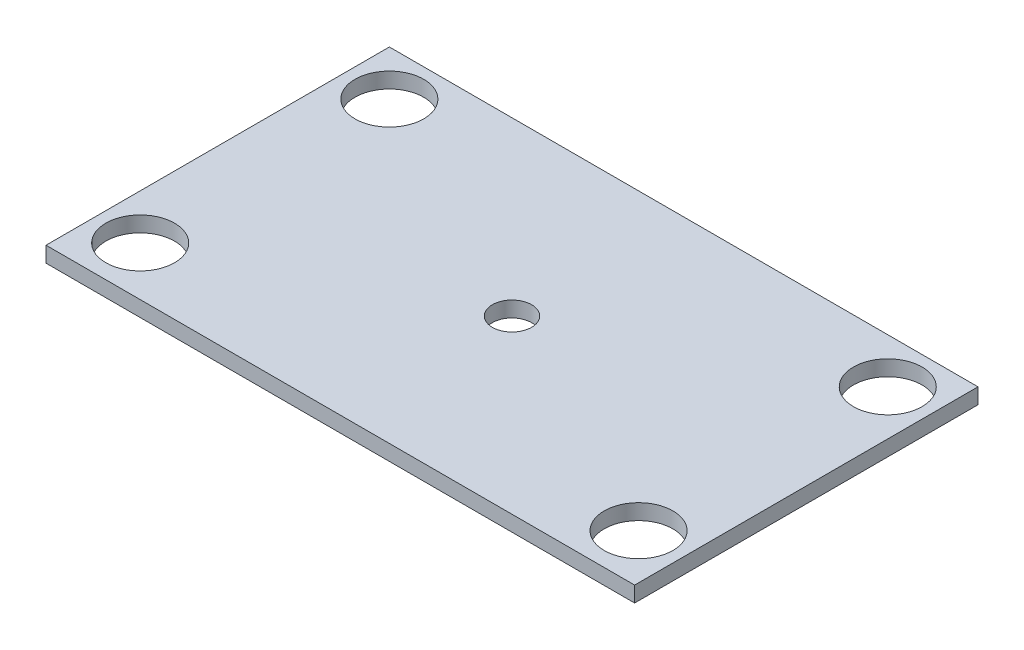
SolidWorks part; units mm, degrees
ref_plane "Front Plane" through (0, 0, 0) normal (0, 0, 1) x (1, 0, 0)
ref_plane "Top Plane" through (0, 0, 0) normal (0, 1, 0) x (1, 0, 0)
ref_plane "Right Plane" through (0, 0, 0) normal (1, 0, 0) x (0, 0, -1)
sketch "Sketch1" plane through (0, 0, 0) normal (0, 1, 0) x (1, 0, 0)
  line L0 (4.6, 30.4) -> (0, 30.4) construction
  line L1 (0, 0) -> (60, 0)
  line L2 (0, 0) -> (0, 35)
  line L3 (0, 35) -> (60, 35)
  line L4 (60, 0) -> (60, 35)
  line L5 (4.6, 30.4) -> (55.4, 30.4) construction
  line L6 (4.6, 30.4) -> (4.6, 5) construction
  line L7 (4.6, 5) -> (55.4, 5) construction
  line L8 (55.4, 30.4) -> (55.4, 5) construction
  line L9 (4.6, 30.4) -> (4.6, 35) construction
  circle A0 centre (4.6, 30.4) radius 3.5
  circle A1 centre (55.4, 30.4) radius 3.5
  circle A2 centre (4.6, 5) radius 3.5
  circle A3 centre (55.4, 5) radius 3.5
  circle A4 centre (30, 17.5) radius 2
  point P13 (30, 30.4)
  point P14 (30, 35)
  point P20 (60, 17.5)
  dimension "D5" = 7
  dimension "D6" = 4
  dimension "D1" = 60
  dimension "D2" = 35
  dimension "D3" = 50.8
  dimension "D4" = 25.4
extrude "Boss-Extrude1" add sketch "Sketch1" along normal blind 1.5875
